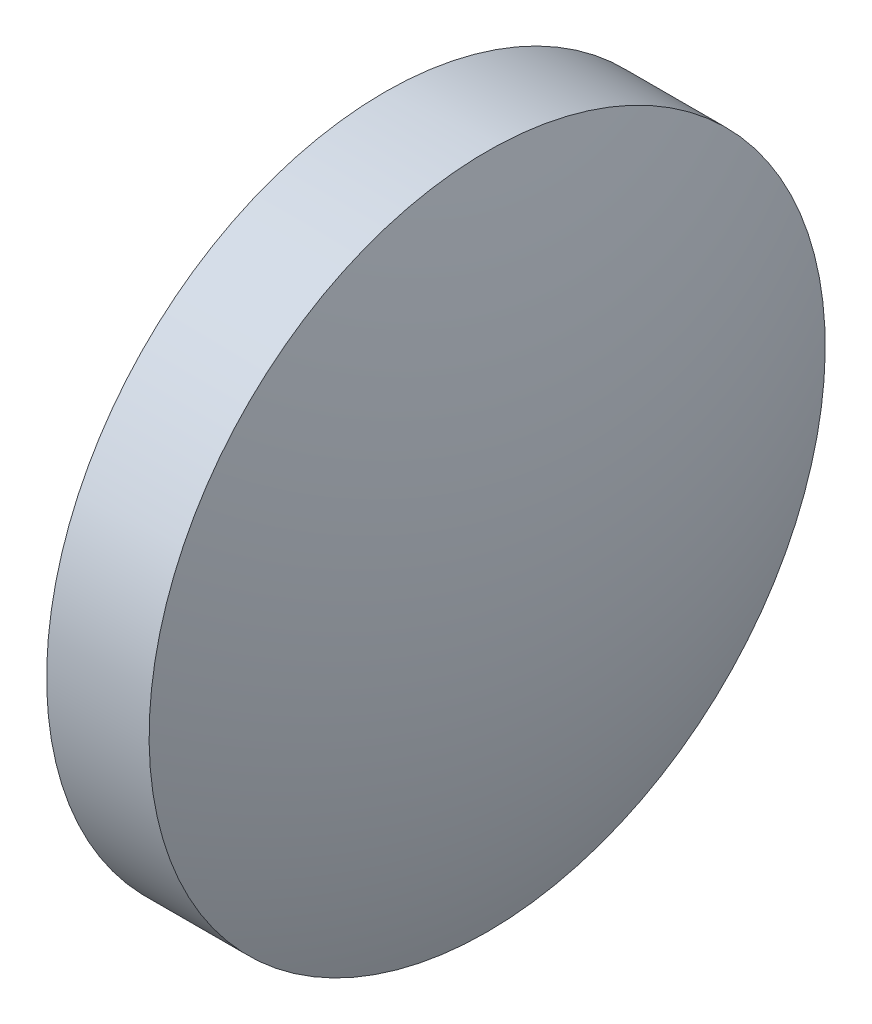
SolidWorks part; units mm, degrees
ref_plane "前视基准面" through (0, 0, 0) normal (0, 0, 1) x (1, 0, 0)
ref_plane "上视基准面" through (0, 0, 0) normal (0, 1, 0) x (1, 0, 0)
ref_plane "右视基准面" through (0, 0, 0) normal (1, 0, 0) x (0, 0, -1)
sketch "草图1" plane through (0, 0, 0) normal (0, 0, 1) x (1, 0, 0)
  line L0 (43.2654, 31.3824) -> (45.2354, 31.3824)
  line L1 (45.2354, 31.3824) -> (45.2354, 18.3823)
  line L2 (45.2354, 18.3823) -> (43.2654, 18.3823)
  line L3 (43.2654, 18.3823) -> (43.2654, 31.3824)
  line L4 (40.96, 24.8823) -> (47.3493, 24.8823) construction
  arc A0 (43.2654, 31.3824) -> (43.2654, 18.3823) centre (60.0448, 24.8823) ccw
  arc A1 (45.2354, 18.3823) -> (45.2354, 31.3824) centre (28.456, 24.8823) ccw
  dimension "D1" = 1.97
  dimension "D2" = 13
revolve "旋转1" add sketch "草图1" angle 360 about L4
